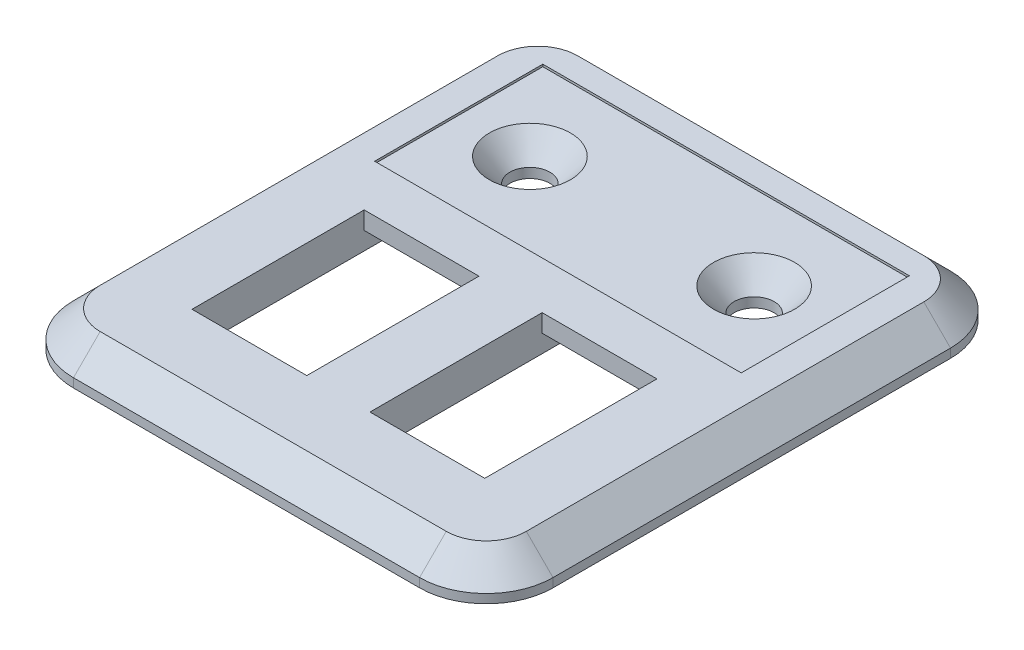
SolidWorks part; units mm, degrees
ref_plane "Front Plane" through (0, 0, 0) normal (0, 0, 1) x (1, 0, 0)
ref_plane "Top Plane" through (0, 0, 0) normal (0, 1, 0) x (1, 0, 0)
ref_plane "Right Plane" through (0, 0, 0) normal (1, 0, 0) x (0, 0, -1)
sketch "Sketch1" plane through (0, 0, 0) normal (0, 1, 0) x (1, 0, 0)
  line L7 (-26.95, -20) -> (26.95, -20)
  line L8 (-26.95, -20) -> (-26.95, 39.675)
  line L9 (-26.95, 39.675) -> (26.95, 39.675)
  line L10 (26.95, -20) -> (26.95, 39.675)
  line L13 (3.55, -9.675) -> (16.45, -9.675)
  line L14 (3.55, -9.675) -> (3.55, 9.675)
  line L15 (3.55, 9.675) -> (16.45, 9.675)
  line L16 (16.45, -9.675) -> (16.45, 9.675)
  line L17 (3.55, -9.675) -> (16.45, 9.675) construction
  line L18 (3.55, 9.675) -> (16.45, -9.675) construction
  line L19 (-16.45, -9.675) -> (-3.55, -9.675)
  line L20 (-16.45, -9.675) -> (-16.45, 9.675)
  line L21 (-16.45, 9.675) -> (-3.55, 9.675)
  line L22 (-3.55, -9.675) -> (-3.55, 9.675)
  line L23 (-16.45, -9.675) -> (-3.55, 9.675) construction
  line L24 (-16.45, 9.675) -> (-3.55, -9.675) construction
  point P0 (0, 0)
  point P1 (0, 0)
  point P2 (0, -20)
  point P6 (0, 0)
  point P11 (10, 0)
  point P16 (-10, 0)
  point P21 (0, 0)
  dimension "D1" = 12.9
  dimension "D2" = 10
  dimension "D3" = 10
  dimension "D4" = 19.35
  dimension "D5" = 30
  dimension "D6" = 10.5
  dimension "D7" = 20
extrude "Boss-Extrude1" add sketch "Sketch1" against normal blind 4
fillet "Fillet1" radius 7.5 4 edges at (26.95, -2, -39.675) (-26.95, -2, -39.675) (26.95, -2, 20) (-26.95, -2, 20)
chamfer "Chamfer1" distance 3 angle 45 8 edges at (0, 0, -39.675) (-24.7533, 0, -37.4783) (24.7533, 0, -37.4783) (-26.95, 0, -9.8375) (26.95, 0, -9.8375) (-24.7533, 0, 17.8033) (24.7533, 0, 17.8033) (0, 0, 20)
sketch "Sketch4" plane through (0, 0, 0) normal (0, 1, 0) x (1, 0, 0)
  line L0 (-16.45, 9.675) -> (-3.55, -9.675) construction
  line L7 (-16.45, -12) -> (-3.55, -12)
  line L8 (-16.45, -12) -> (-16.45, 12)
  line L9 (-16.45, 12) -> (-3.55, 12)
  line L10 (-3.55, -12) -> (-3.55, 12)
  line L11 (-16.45, -12) -> (-3.55, 12) construction
  line L12 (-16.45, 12) -> (-3.55, -12) construction
  line L14 (3.55, -12) -> (16.45, -12)
  line L15 (3.55, -12) -> (3.55, 12)
  line L16 (3.55, 12) -> (16.45, 12)
  line L17 (16.45, -12) -> (16.45, 12)
  line L18 (3.55, -12) -> (16.45, 12) construction
  line L19 (3.55, 12) -> (16.45, -12) construction
  point P0 (0, 0)
  point P6 (-10, 0)
  point P13 (10, 0)
  dimension "D1" = 24
extrude "Cut-Extrude1" cut sketch "Sketch4" against normal through all from offset 2 offset against normal yes
sketch "Sketch5" plane through (0, 0, 0) normal (0, 1, 0) x (1, 0, 0)
  line L1 (-20.6, 15) -> (20.6, 15)
  line L2 (-20.6, 15) -> (-20.6, 33.9)
  line L3 (-20.6, 33.9) -> (20.6, 33.9)
  line L4 (20.6, 15) -> (20.6, 33.9)
  line L5 (-20.6, 15) -> (20.6, 33.9) construction
  line L6 (-20.6, 33.9) -> (20.6, 15) construction
  point P0 (0, 24.45)
  point P5 (0, 0)
  dimension "D1" = 18.9
  dimension "D2" = 15
  dimension "D3" = 41.2
extrude "Cut-Extrude2" cut sketch "Sketch5" against normal blind 0.25
hole_wizard "CSK for #8 Flat Head Socket Cap Screw1" positions "Sketch2" profile "Sketch3" countersink size "#8" standard "ANSI Inch" end condition through all
sketch "Sketch2" plane through (0, -0.25, 0) normal (0, 1, 0) x (1, 0, 0)
  line L0 (-20.6, 33.9) -> (-20.6, 15) construction
  line L1 (20.6, 15) -> (20.6, 33.9) construction
  point P13 (-12.6, 24.45)
  point P15 (12.6, 24.45)
  point P22 (0, 0)
  point P23 (0, 0)
  dimension "D1" = 8
  dimension "D2" = 8
sketch "Sketch3" plane through (-12.6, -0.25, -24.45) normal (1, 0, 0) x (0, 0, 1)
  line L0 (0, 0) -> (0, 3.75)
  line L1 (0, 3.75) -> (2.2479, 3.75)
  line L2 (2.2479, 3.75) -> (2.2479, 2.659)
  line L3 (2.2479, 2.659) -> (4.5593, 0)
  line L5 (4.5593, 0) -> (0, 0)
  line L6 (-2.2479, 2.659) -> (-4.5593, 0) construction
  line L11 (0, -6.35) -> (0, 107.95) construction
  dimension "Thru Hole Dia." = 4.4958
  dimension "Thru Hole Depth" = 3.75
  dimension "Near C'Sink Dia." = 9.1186
  dimension "Near C'Sink Angle" = 82
